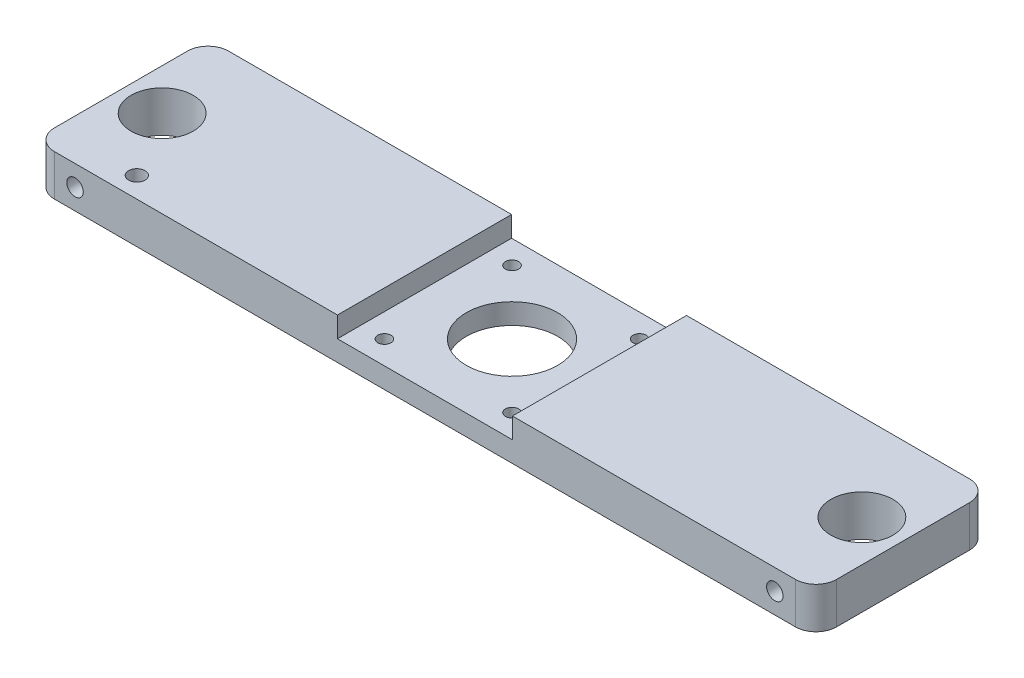
SolidWorks part; units mm, degrees
ref_plane "前视基准面" through (0, 0, 0) normal (0, 0, 1) x (1, 0, 0)
ref_plane "上视基准面" through (0, 0, 0) normal (0, 1, 0) x (1, 0, 0)
ref_plane "右视基准面" through (0, 0, 0) normal (1, 0, 0) x (0, 0, -1)
sketch "草图1" plane through (0, 0, 0) normal (0, 1, 0) x (1, 0, 0)
  line L1 (-95, 21.15) -> (95, 21.15)
  line L2 (-95, 21.15) -> (-95, -21.15)
  line L3 (-95, -21.15) -> (95, -21.15)
  line L4 (95, 21.15) -> (95, -21.15)
  line L5 (-95, 21.15) -> (95, -21.15) construction
  line L6 (-95, -21.15) -> (95, 21.15) construction
  point P0 (0, 0)
  dimension "D1" = 190
  dimension "D2" = 42.3
extrude "凸台-拉伸1" add sketch "草图1" along normal blind 10
sketch "草图2" plane through (0, 10, 0) normal (0, 1, 0) x (1, 0, 0)
  line L1 (-21.25, 38.5265) -> (21.25, 38.5265)
  line L2 (-21.25, 38.5265) -> (-21.25, -38.5265)
  line L3 (-21.25, -38.5265) -> (21.25, -38.5265)
  line L4 (21.25, 38.5265) -> (21.25, -38.5265)
  line L5 (-21.25, 38.5265) -> (21.25, -38.5265) construction
  line L6 (-21.25, -38.5265) -> (21.25, 38.5265) construction
  point P0 (0, 0)
  dimension "D1" = 42.5
extrude "切除-拉伸1" cut sketch "草图2" against normal blind 5
sketch "草图3" plane through (0, 5, 0) normal (0, 1, 0) x (1, 0, 0)
  line L0 (0, 0) -> (0, 24.4253) construction
  line L1 (0, 0) -> (27.5231, 0) construction
  circle A0 centre (-15.5, 15.5) radius 1.6
  circle A1 centre (15.5, 15.5) radius 1.6
  circle A2 centre (15.5, -15.5) radius 1.6
  circle A3 centre (-15.5, -15.5) radius 1.6
  circle A4 centre (0, 0) radius 11.1
  dimension "D3" = 22.2
  dimension "D4" = 3.2
  dimension "D1" = 31
  dimension "D2" = 31
extrude "切除-拉伸2" cut sketch "草图3" against normal through all
sketch "草图4" plane through (0, 10, 0) normal (0, 1, 0) x (1, 0, 0)
  line L0 (0, 0) -> (0, 47.7289) construction
  circle A0 centre (-85, 0) radius 7.55
  circle A1 centre (85, 0) radius 7.55
  dimension "D1" = 15.1
  dimension "D2" = 170
extrude "切除-拉伸3" cut sketch "草图4" against normal through all
fillet "圆角1" radius 5 4 edges at (95, 5, -21.15) (95, 5, 21.15) (-95, 5, 21.15) (-95, 5, -21.15)
sketch "草图5" plane through (0, 0, 21.15) normal (0, 0, 1) x (1, 0, 0)
  line L0 (-95, 0) -> (-95, 10) construction
  line L1 (95, 10) -> (95, 0) construction
  line L2 (21.25, 10) -> (90, 10) construction
  line L3 (-90, 10) -> (-21.25, 10) construction
  circle A0 centre (85, 5) radius 2
  circle A1 centre (-85, 5) radius 2
  dimension "D1" = 4
  dimension "D2" = 4
  dimension "D3" = 10
  dimension "D4" = 10
  dimension "D5" = 5
  dimension "D6" = 5
extrude "切除-拉伸4" cut sketch "草图5" against normal up to next
sketch "草图6" plane through (0, 10, 0) normal (0, 1, 0) x (1, 0, 0)
  line L0 (-90, -21.15) -> (-21.25, -21.15) construction
  line L1 (-95, 16.15) -> (-95, -16.15) construction
  circle A0 centre (-75, -16.15) radius 2
  dimension "D1" = 4
  dimension "D2" = 5
  dimension "D3" = 20
extrude "切除-拉伸5" cut sketch "草图6" against normal through all
